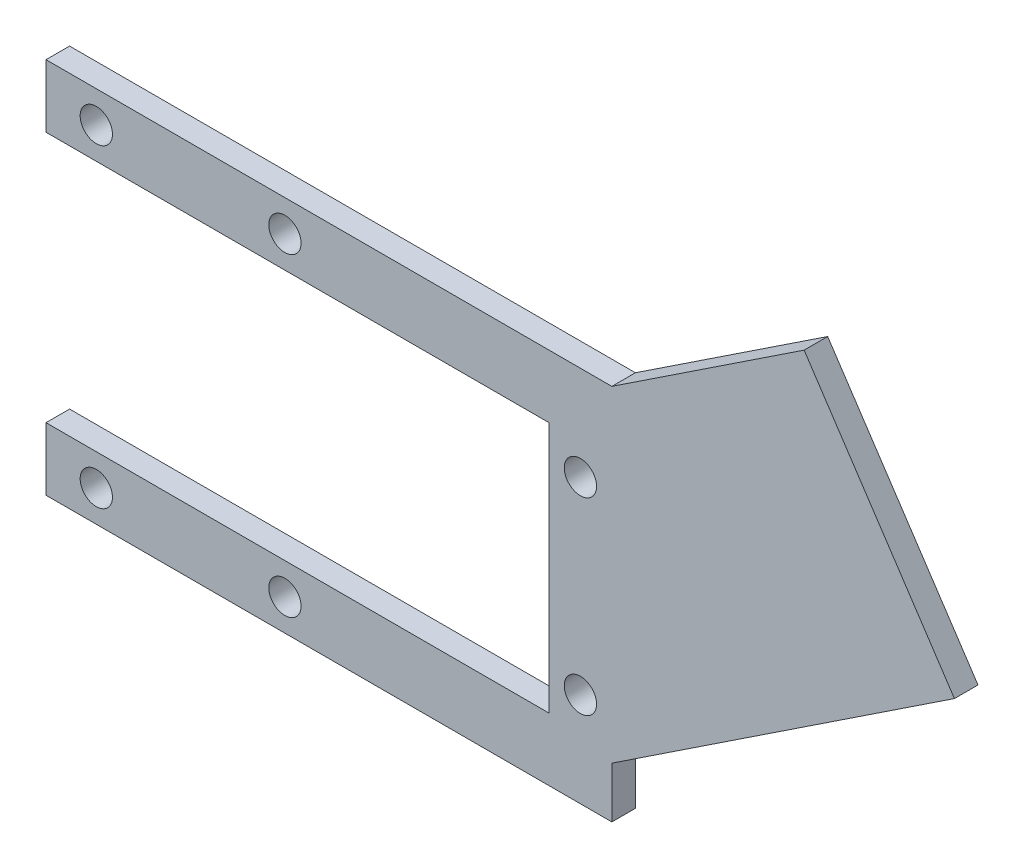
SolidWorks part; units mm, degrees
ref_plane "Front Plane" through (0, 0, 0) normal (0, 0, 1) x (1, 0, 0)
ref_plane "Top Plane" through (0, 0, 0) normal (0, 1, 0) x (1, 0, 0)
ref_plane "Right Plane" through (0, 0, 0) normal (1, 0, 0) x (0, 0, -1)
sketch "Sketch1" plane through (0, 0, 0) normal (0, 0, 1) x (1, 0, 0)
  line L0 (0, 0) -> (101.6, 0)
  line L1 (101.6, 0) -> (101.6, -50.8)
  line L2 (101.6, -50.8) -> (0, -50.8)
  line L3 (0, -50.8) -> (0, -63.5)
  line L4 (0, -63.5) -> (114.3, -63.5)
  line L6 (114.3, 12.7) -> (0, 12.7)
  line L7 (0, 12.7) -> (0, 0)
  line L9 (153.1382, 38.4574) -> (183.4993, -7.3224)
  line L10 (183.4993, -7.3224) -> (114.3, -53.2153)
  line L11 (114.3, -53.2153) -> (114.3, -63.5)
  line L13 (114.3, 12.7) -> (153.1382, 38.4574)
  circle A0 centre (10.16, 6.35) radius 3.2639
  circle A1 centre (48.26, 6.35) radius 3.2639
  circle A2 centre (10.16, -57.15) radius 3.2639
  circle A3 centre (48.26, -57.15) radius 3.2639
  point P21 (0, -57.15)
  point P22 (114.3, 2.4153)
  point P23 (114.3, 11.9462)
  point P24 (0, 6.35)
  dimension "D3" = 6.5278
  dimension "D1" = 50.8
  dimension "D2" = 12.7
  dimension "D4" = 38.1
  dimension "D5" = 10.16
  dimension "D6" = 114.3
  dimension "D7" = 12.7
extrude "Boss-Extrude1" add sketch "Sketch1" along normal blind 4.7625
sketch "Sketch2" plane through (0, 0, 4.7625) normal (0, 0, 1) x (1, 0, 0)
  line L0 (101.6, 0) -> (101.6, -50.8) construction
  circle A0 centre (107.95, -6.35) radius 3.2639
  circle A1 centre (107.95, -44.45) radius 3.2639
  point P5 (101.6, -25.4)
  dimension "D1" = 6.5278
  dimension "D2" = 38.1
  dimension "D3" = 19.05
  dimension "D4" = 6.35
extrude "Cut-Extrude1" cut sketch "Sketch2" against normal up to next
